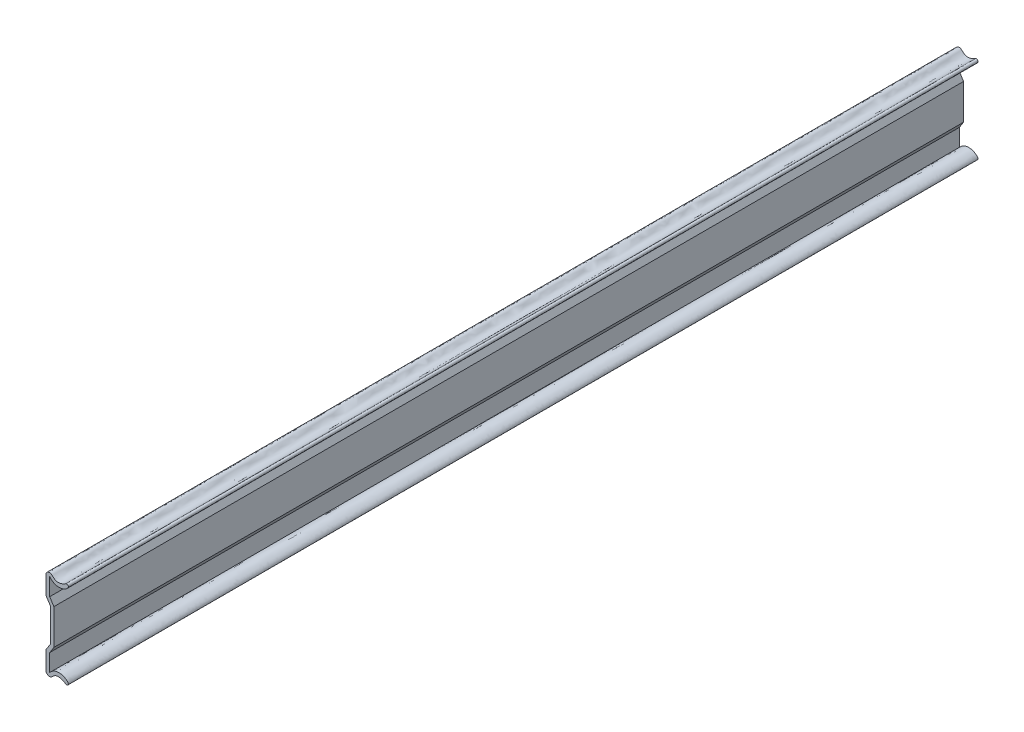
SolidWorks part; units mm, degrees
material "6061 Alloy"
ref_plane "Front Plane" through (0, 0, 0) normal (0, 0, 1) x (1, 0, 0)
ref_plane "Top Plane" through (0, 0, 0) normal (0, 1, 0) x (1, 0, 0)
ref_plane "Right Plane" through (0, 0, 0) normal (1, 0, 0) x (0, 0, -1)
sketch "Sketch1" plane through (0, 0, 0) normal (0, 0, 1) x (1, 0, 0)
  line L0 (3.9981, 3930.1943) -> (3.9981, 3942.6139)
  line L1 (3.6614, 3952.1953) -> (3.6614, 3945.6067)
  line L2 (3.6614, 3945.6067) -> (5.2393, 3943.1194)
  line L3 (5.2393, 3943.1194) -> (5.2393, 3929.6888)
  line L4 (5.2393, 3929.6888) -> (3.6614, 3927.2015)
  line L5 (3.6614, 3927.2015) -> (3.6614, 3920.613)
  line L6 (2.2472, 3927.5247) -> (3.9981, 3930.1943)
  line L7 (3.9981, 3942.6139) -> (2.2472, 3945.2835)
  spline S0 degree 3 poles (3.6614, 3920.613) (4.8601, 3921.9816) (6.0157, 3922.2907) (7.2504, 3922.3606) (7.5302, 3922.3544) (8.4533, 3922.2508) (9.0248, 3922.0218) (9.7786, 3921.5593) (9.7854, 3921.5551) (11.5677, 3920.4535) (10.4179, 3919.3767) (9.6335, 3919.9605) knots 0 0 0 0 0.375 0.375 0.5 0.5 0.811035 0.811035 0.811523 0.811523 1 1 1 1
  spline S1 degree 3 poles (9.6335, 3919.9605) (9.2709, 3920.2304) (8.7162, 3920.5012) (7.8707, 3920.7697) (7.5881, 3920.8353) (6.7913, 3920.9361) (6.3165, 3920.8839) (5.7281, 3920.6556) (5.5543, 3920.5525) (5.0832, 3920.1995) (4.5813, 3919.6208) (4.0478, 3919.339) (3.6216, 3919.2843) (3.4741, 3919.2933) (2.9857, 3919.4109) (2.6449, 3919.619) (2.4373, 3919.8542) (2.4185, 3919.8769) (2.2324, 3920.1635) (2.2472, 3920.8029) (2.2472, 3927.5247) knots 0 0 0 0 0.125 0.125 0.1875 0.1875 0.3125 0.3125 0.375 0.375 0.5 0.625 0.625 0.6875 0.6875 0.828125 0.828125 0.84375 0.84375 1 1 1 1
  spline S2 degree 3 poles (9.6335, 3952.8477) (10.4179, 3953.4316) (11.5677, 3952.3547) (9.7854, 3951.2531) (9.7786, 3951.2489) (9.0248, 3950.7865) (8.4533, 3950.5574) (7.5302, 3950.4539) (7.2504, 3950.4477) (6.0157, 3950.5175) (4.8601, 3950.8266) (3.6614, 3952.1953) knots 0 0 0 0 0.188477 0.188477 0.188965 0.188965 0.5 0.5 0.625 0.625 1 1 1 1
  spline S3 degree 3 poles (2.2472, 3945.2835) (2.2472, 3952.0053) (2.2324, 3952.6448) (2.4185, 3952.9313) (2.4373, 3952.954) (2.6449, 3953.1892) (2.9857, 3953.3973) (3.4741, 3953.5149) (3.6216, 3953.5239) (4.0478, 3953.4692) (4.5813, 3953.1874) (5.0832, 3952.6087) (5.5543, 3952.2557) (5.7281, 3952.1526) (6.3165, 3951.9243) (6.7913, 3951.8721) (7.5881, 3951.973) (7.8707, 3952.0385) (8.7162, 3952.307) (9.2709, 3952.5778) (9.6335, 3952.8477) knots 0 0 0 0 0.15625 0.15625 0.171875 0.171875 0.3125 0.3125 0.375 0.375 0.5 0.625 0.625 0.6875 0.6875 0.8125 0.8125 0.875 0.875 1 1 1 1
extrude "Boss-Extrude1" add sketch "Sketch1" along normal blind 346
sketch "Sketch2" plane through (0, 0, 346) normal (0, 0, 1) x (1, 0, 0)
  line L0 (3.9981, 3936.4041) -> (5.2393, 3936.4041)
  line L1 (3.9981, 3942.6139) -> (3.9981, 3930.1943) construction
  line L2 (5.2393, 3929.6888) -> (5.2393, 3943.1194) construction
ref_plane "Plane1" through (0, 3936.4041, 0) normal (0, -1, 0) x (1, 0, 0)
